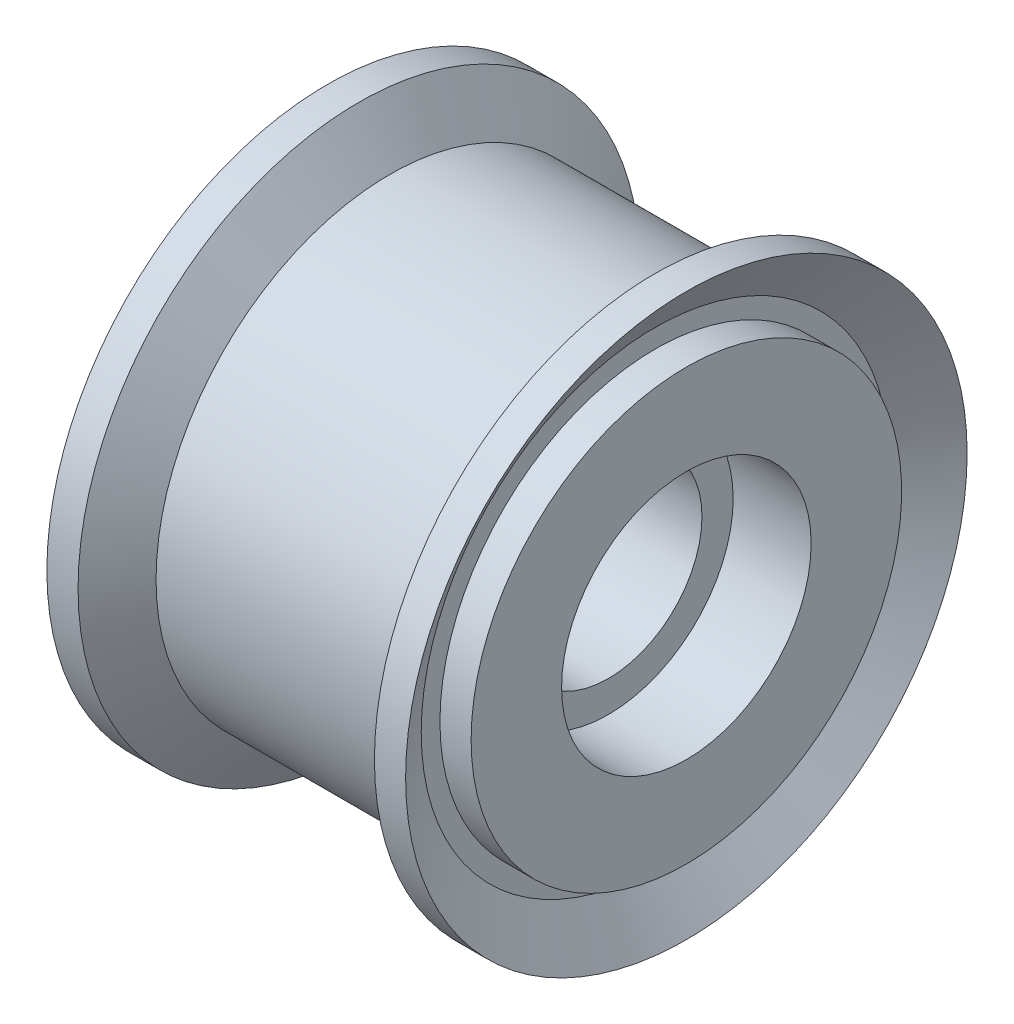
SolidWorks part; units mm, degrees
ref_plane "Front Plane" through (0, 0, 0) normal (0, 0, 1) x (1, 0, 0)
ref_plane "Top Plane" through (0, 0, 0) normal (0, 1, 0) x (1, 0, 0)
ref_plane "Right Plane" through (0, 0, 0) normal (1, 0, 0) x (0, 0, -1)
ref_plane "Plane1" through (0, 0, 0) normal (0, 0, 1) x (1, 0, 0)
sketch "Sketch1" plane through (0, 0, 0) normal (0, 0, 1) x (1, 0, 0)
  line L0 (-5.75, 9) -> (-4.75, 7.5)
  line L1 (-4.75, 7.5) -> (-4.75, 6.9)
  line L2 (-4.75, 6.9) -> (-5.75, 6.9)
  line L3 (-5.75, 6.9) -> (-5.75, 4)
  line L4 (-5.75, 4) -> (-3.25, 4)
  line L5 (-3.25, 4) -> (-3.25, 3)
  line L6 (-3.25, 3) -> (3.25, 3)
  line L7 (3.25, 3) -> (3.25, 4)
  line L8 (3.25, 4) -> (5.75, 4)
  line L9 (5.75, 4) -> (5.75, 6.9)
  line L10 (5.75, 6.9) -> (4.75, 6.9)
  line L11 (4.75, 6.9) -> (4.75, 7.5)
  line L12 (4.75, 7.5) -> (5.75, 9)
  line L13 (5.75, 9) -> (4.75, 9)
  line L14 (4.75, 9) -> (3.75, 7.5)
  line L15 (3.75, 7.5) -> (-3.75, 7.5)
  line L16 (-3.75, 7.5) -> (-4.75, 9)
  line L17 (-4.75, 9) -> (-5.75, 9)
  line L18 (5.75, 0) -> (-5.75, 0) construction
revolve "Revolve1" add sketch "Sketch1" angle 360 about L18
